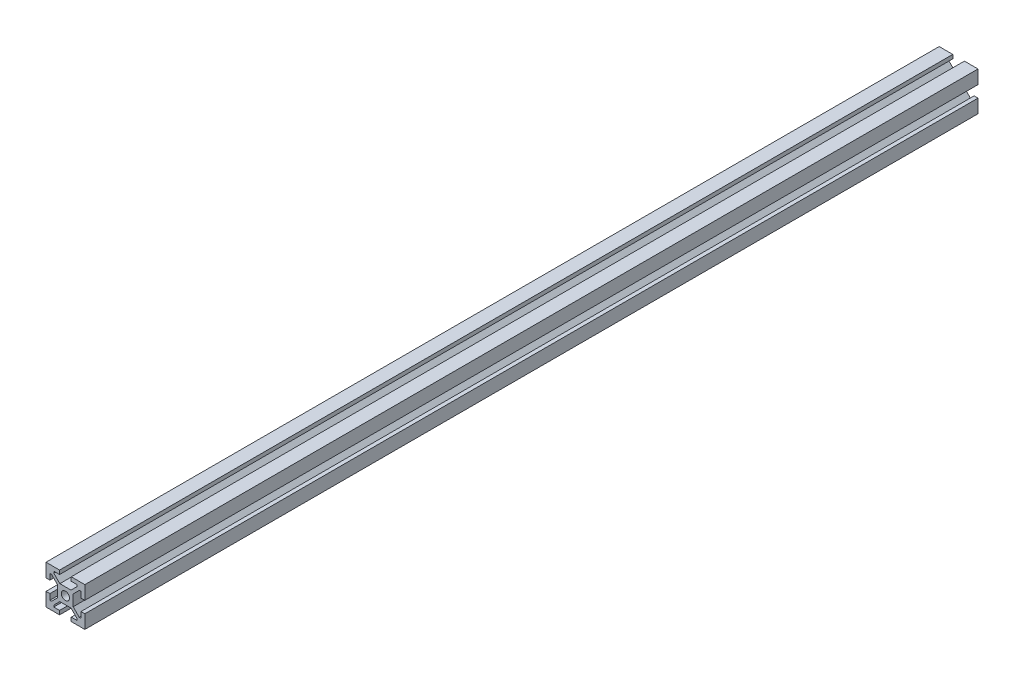
SolidWorks part; units mm, degrees
ref_plane "Alzado" through (0, 0, 0) normal (0, 0, 1) x (1, 0, 0)
ref_plane "Planta" through (0, 0, 0) normal (0, 1, 0) x (1, 0, 0)
ref_plane "Vista lateral" through (0, 0, 0) normal (1, 0, 0) x (0, 0, -1)
ref_plane "Plano1" through (0, 0, 460) normal (0, 0, 1) x (1, 0, 0)
sketch "Croquis1" plane through (0, 0, 460) normal (0, 0, 1) x (1, 0, 0)
  line L0 (-10, 10) -> (-10, 3)
  line L1 (-10, 3) -> (-8, 3)
  line L2 (-8, 3) -> (-8, 6)
  line L3 (-8, 6) -> (-7.1314, 6)
  line L4 (-7.1314, 6) -> (-4, 2.8686)
  line L5 (-4, 2.8686) -> (-4, -2.8686)
  line L6 (-4, -2.8686) -> (-7.1314, -6)
  line L7 (-7.1314, -6) -> (-8, -6)
  line L8 (-8, -6) -> (-8, -3)
  line L9 (-8, -3) -> (-10, -3)
  line L10 (-10, -3) -> (-10, -10)
  line L11 (-10, -10) -> (-3, -10)
  line L12 (-3, -10) -> (-3, -8)
  line L13 (-3, -8) -> (-6, -8)
  line L14 (-6, -8) -> (-6, -7.1314)
  line L15 (-6, -7.1314) -> (-2.8686, -4)
  line L16 (-2.8686, -4) -> (2.8686, -4)
  line L17 (2.8686, -4) -> (6, -7.1314)
  line L18 (6, -7.1314) -> (6, -8)
  line L19 (6, -8) -> (3, -8)
  line L20 (3, -8) -> (3, -10)
  line L21 (3, -10) -> (10, -10)
  line L22 (10, -10) -> (10, -3)
  line L23 (10, -3) -> (8, -3)
  line L24 (8, -3) -> (8, -6)
  line L25 (8, -6) -> (7.1314, -6)
  line L26 (7.1314, -6) -> (4, -2.8686)
  line L27 (4, -2.8686) -> (4, 2.8686)
  line L28 (4, 2.8686) -> (7.1314, 6)
  line L29 (7.1314, 6) -> (8, 6)
  line L30 (8, 6) -> (8, 3)
  line L31 (8, 3) -> (10, 3)
  line L32 (10, 3) -> (10, 10)
  line L33 (10, 10) -> (3, 10)
  line L34 (3, 10) -> (3, 8)
  line L35 (3, 8) -> (6, 8)
  line L36 (6, 8) -> (6, 7.1314)
  line L37 (6, 7.1314) -> (2.8686, 4)
  line L38 (2.8686, 4) -> (-2.8686, 4)
  line L39 (-2.8686, 4) -> (-6, 7.1314)
  line L40 (-6, 7.1314) -> (-6, 8)
  line L41 (-6, 8) -> (-3, 8)
  line L42 (-3, 8) -> (-3, 10)
  line L43 (-3, 10) -> (-10, 10)
  circle A0 centre (0, 0) radius 2.1
extrude "Saliente-Extruir1" add sketch "Croquis1" against normal blind 460
cosmetic thread "Rosca cosmética1" parameters "D1"=12, "D2"=5
cosmetic thread "Rosca cosmética2" parameters "D1"=12, "D2"=5
sketch "Croquis2" plane through (10, 0, 0) normal (1, 0, 0) x (0, 0, -1)
  line L0 (0, -10) -> (0, -3) construction
  line L1 (0, 0) -> (-460, 0) construction
  line L2 (-460, -2.8686) -> (-460, 2.8686) construction
  line L3 (-460, 3) -> (-460, 10) construction
  circle A0 centre (-128.4, 0) radius 2.75
  circle A1 centre (-331.6, 0) radius 2.75
  circle A2 centre (-450, 0) radius 2.75
  circle A3 centre (-10, 0) radius 2.75
  dimension "D1" = 128.4
  dimension "D2" = 128.4
  dimension "D3" = 5.5
  dimension "D4" = 10
  dimension "D5" = 10
extrude "Cortar-Extruir1" cut sketch "Croquis2" against normal through all
